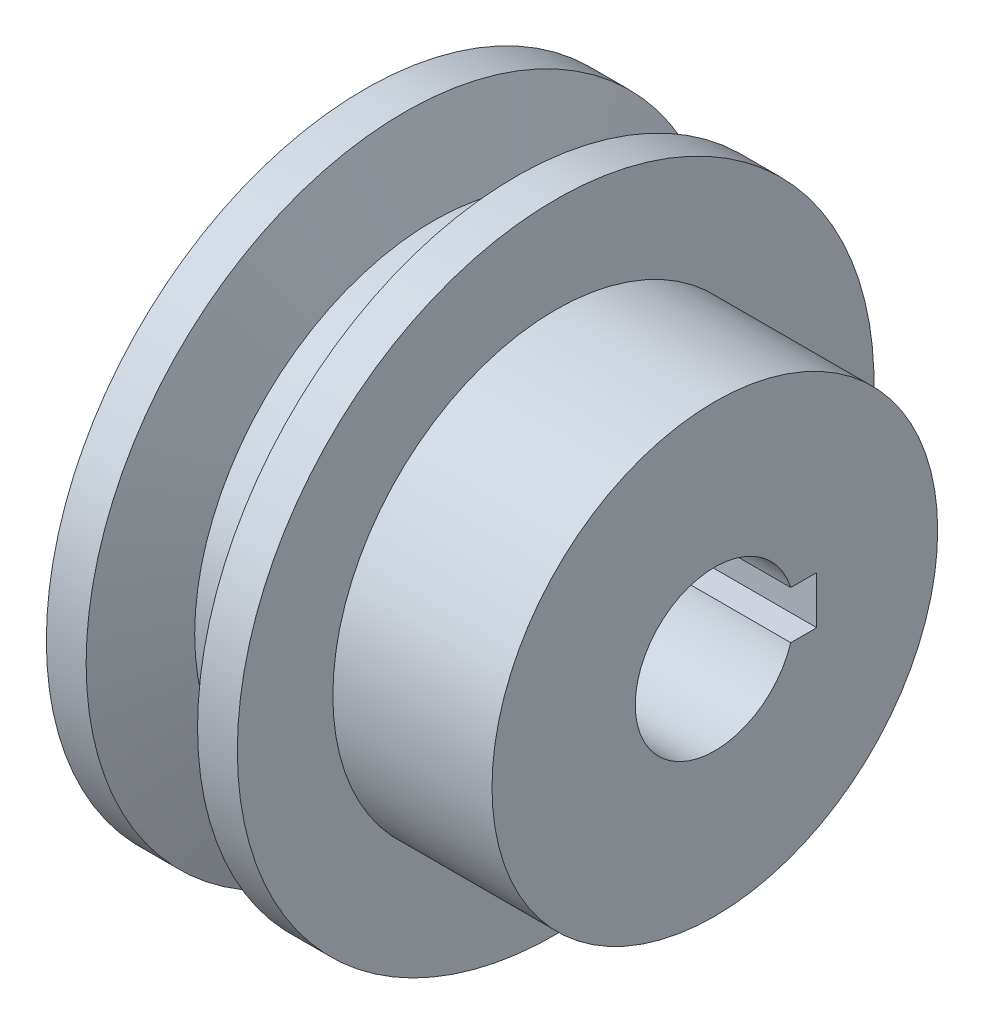
SolidWorks part; units mm, degrees
ref_plane "Front Plane" through (0, 0, 0) normal (0, 0, 1) x (1, 0, 0)
ref_plane "Top Plane" through (0, 0, 0) normal (0, 1, 0) x (1, 0, 0)
ref_plane "Right Plane" through (0, 0, 0) normal (1, 0, 0) x (0, 0, -1)
sketch "Sketch1" plane through (0, 0, 0) normal (0, 0, 1) x (1, 0, 0)
  line L0 (-16.5108, 0) -> (25.0495, 0) construction
  line L1 (-6.5628, 5) -> (-6.5628, 20)
  line L2 (-6.5628, 20) -> (-4.0628, 20)
  line L3 (-4.0628, 20) -> (-2.243, 15)
  line L4 (-2.243, 15) -> (1.1173, 15)
  line L5 (1.1173, 15) -> (2.9372, 20)
  line L6 (2.9372, 20) -> (5.4372, 20)
  line L7 (5.4372, 20) -> (5.4372, 14)
  line L8 (5.4372, 14) -> (15.4372, 14)
  line L9 (15.4372, 14) -> (15.4372, 5)
  line L10 (15.4372, 5) -> (-6.5628, 5)
  point P14 (-0.5628, 15)
  point P15 (-5.3128, 20)
  dimension "D1" = 15
  dimension "D2" = 14
  dimension "D3" = 5
  dimension "D4" = 12
  dimension "D5" = 22
  dimension "D6" = 7
  dimension "D7" = 2.5
  dimension "D8" = 40
  dimension "D9" = 6
  dimension "D10" = 6
revolve "Revolve1" add sketch "Sketch1" angle 360 about L0
sketch "Sketch2" plane through (15.4372, 0, 0) normal (1, 0, 0) x (0, 0, -1)
  line L0 (4.7697, -1.5) -> (6.4, -1.5)
  line L1 (6.4, -1.5) -> (6.4, 1.5)
  line L2 (6.4, 1.5) -> (4.7697, 1.5)
  circle A0 centre (0, 0) radius 5 construction
  arc A1 (4.7697, -1.5) -> (4.7697, 1.5) centre (0, 0) ccw
  point P6 (6.4, 0)
  dimension "D1" = 6.4
  dimension "D2" = 3
extrude "Cut-Extrude1" cut sketch "Sketch2" against normal through all both and the other way through all
